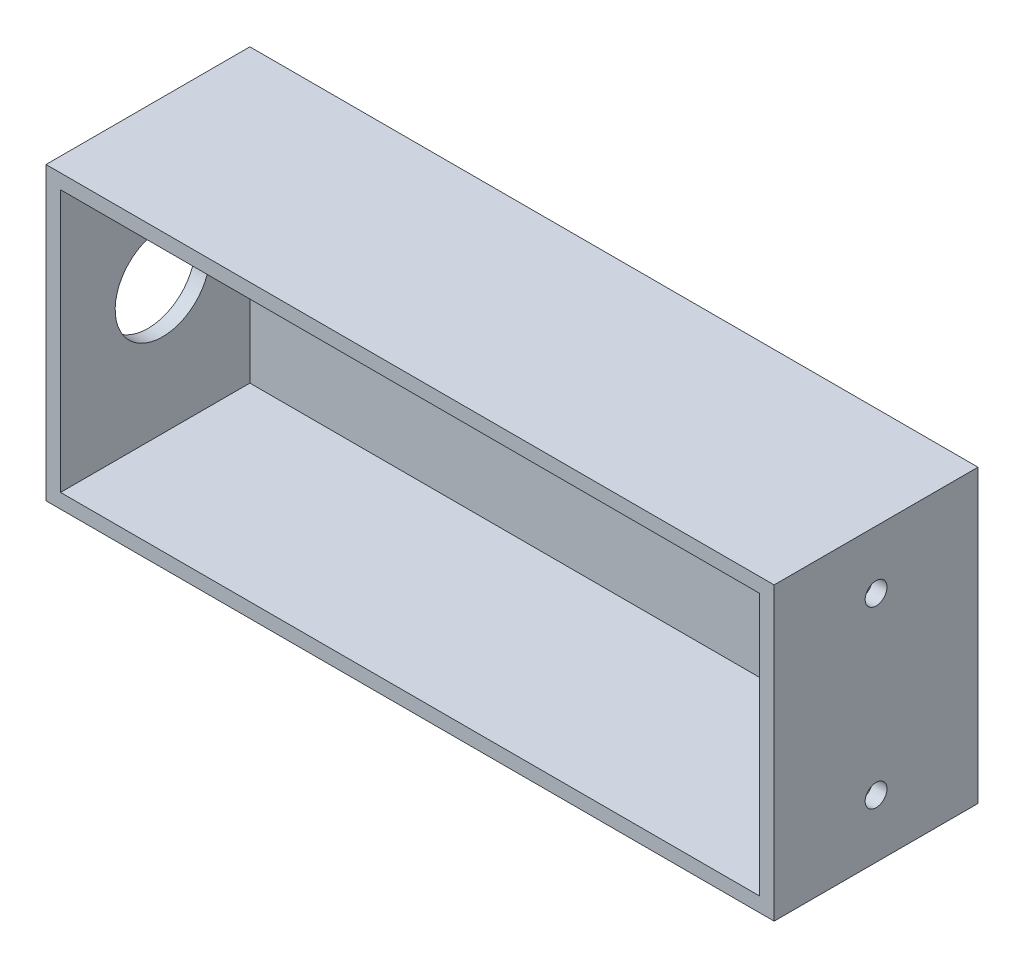
SolidWorks part; units mm, degrees
ref_plane "前视基准面" through (0, 0, 0) normal (0, 0, 1) x (1, 0, 0)
ref_plane "上视基准面" through (0, 0, 0) normal (0, 1, 0) x (1, 0, 0)
ref_plane "右视基准面" through (0, 0, 0) normal (1, 0, 0) x (0, 0, -1)
sketch "草图2" plane through (0, 0, 0) normal (0, 0, 1) x (1, 0, 0)
  line L1 (-100, 40) -> (100, 40)
  line L2 (-100, 40) -> (-100, -40)
  line L3 (-100, -40) -> (100, -40)
  line L4 (100, 40) -> (100, -40)
  line L5 (-100, 40) -> (100, -40) construction
  line L6 (-100, -40) -> (100, 40) construction
  point P0 (0, 0)
  dimension "D1" = 200
  dimension "D2" = 80
extrude "凸台-拉伸1" add sketch "草图2" along normal blind 56
sketch "草图3" plane through (0, 0, 56) normal (0, 0, 1) x (1, 0, 0)
  line L1 (-96, 36) -> (96, 36)
  line L2 (-96, 36) -> (-96, -36)
  line L3 (-96, -36) -> (96, -36)
  line L4 (96, 36) -> (96, -36)
  line L5 (-96, 36) -> (96, -36) construction
  line L6 (-96, -36) -> (96, 36) construction
  point P0 (0, 0)
  dimension "D1" = 192
  dimension "D2" = 72
extrude "切除-拉伸1" cut sketch "草图3" against normal blind 52
ref_plane "基准面2" through (-100, 0, 0) normal (-1, 0, 0) x (0, 0, 1)
sketch "草图6" plane through (-100, 0, 0) normal (-1, 0, 0) x (0, 0, 1)
  line L0 (0, 40) -> (0, -40) construction
  circle A0 centre (28, 0) radius 13
  point P4 (0, 0)
  dimension "D2" = 26
  dimension "D1" = 28
extrude "切除-拉伸2" cut sketch "草图6" against normal up to surface (4 mm away) up to face at (-96, 0, 30)
ref_plane "基准面3" through (100, 0, 0) normal (1, 0, 0) x (0, 0, -1)
sketch "草图8" plane through (100, 0, 0) normal (1, 0, 0) x (0, 0, -1)
  line L0 (-28, 24) -> (-28, -24) construction
  line L1 (-56, 40) -> (0, 40) construction
  circle A0 centre (-28, 0) radius 12.3294 construction
  circle A1 centre (-28, 24) radius 3
  circle A2 centre (-28, -24) radius 3
  point P4 (-28, 0)
  point P10 (0, 0)
  point P11 (-28, 40)
  dimension "D2" = 6
  dimension "D3" = 6
  dimension "D1" = 48
extrude "切除-拉伸3" cut sketch "草图8" against normal blind 10
